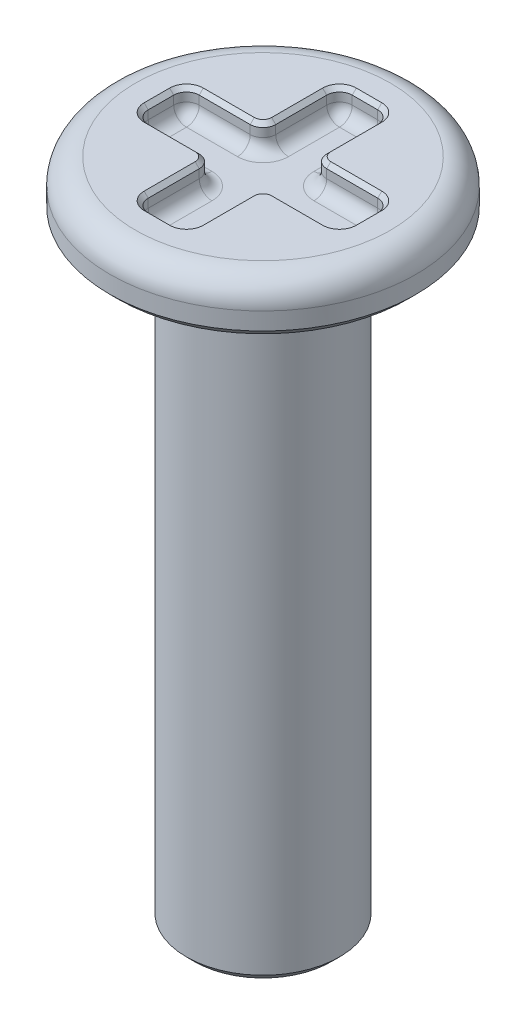
SolidWorks part; units mm, degrees
ref_plane "Front Plane" through (0, 0, 0) normal (0, 0, 1) x (1, 0, 0)
ref_plane "Top Plane" through (0, 0, 0) normal (0, 1, 0) x (1, 0, 0)
ref_plane "Right Plane" through (0, 0, 0) normal (1, 0, 0) x (0, 0, -1)
sketch "Sketch1" plane through (0, 0, 0) normal (0, 0, 1) x (1, 0, 0)
  line L0 (0, 5.1735) -> (0, 4.4648) construction
  line L1 (0, 0) -> (2.3813, 0)
  line L2 (2.3813, 0) -> (2.3813, 19.05)
  line L3 (2.3813, 19.05) -> (4.7625, 19.05)
  line L4 (4.7625, 19.05) -> (4.7625, 20.6375)
  line L5 (4.7625, 20.6375) -> (0, 20.6375)
  line L6 (0, 20.6375) -> (0, 0)
  dimension "D1" = 4.7625
  dimension "D2" = 19.05
  dimension "D3" = 1.5875
  dimension "D4" = 9.525
revolve "Revolve1" add sketch "Sketch1" angle 360 about L0
sketch "Sketch2" plane through (0, 20.6375, 0) normal (0, 1, 0) x (1, 0, 0)
  line L0 (-3.175, 0.7937) -> (-0.7938, 0.7937)
  line L1 (-0.7938, 0.7937) -> (-0.7937, 3.175)
  line L2 (-0.7937, 3.175) -> (0.7937, 3.175)
  line L3 (0.7937, 3.175) -> (0.7937, 0.7938)
  line L4 (0.7937, 0.7938) -> (3.175, 0.7937)
  line L5 (3.175, 0.7937) -> (3.175, -0.7937)
  line L6 (3.175, -0.7937) -> (0.7938, -0.7938)
  line L7 (0.7938, -0.7938) -> (0.7937, -3.175)
  line L8 (0.7937, -3.175) -> (-0.7937, -3.175)
  line L9 (-0.7937, -3.175) -> (-0.7938, -0.7938)
  line L10 (-0.7938, -0.7938) -> (-3.175, -0.7937)
  line L11 (-3.175, -0.7937) -> (-3.175, 0.7937)
  line L12 (0, -3.175) -> (0, 3.175) construction
  line L13 (3.175, 0) -> (-3.175, 0) construction
  dimension "D1" = 1.5875
  dimension "D2" = 6.35
extrude "Cut-Extrude1" cut sketch "Sketch2" against normal blind 0.7937 contours L1 L2 L3 L4 L5 L6 L7 L8 L9 L10 L11 L0
fillet "Fillet2" radius 0.7937 2 edges at (0, 20.6375, 4.7625) (0, 19.05, 2.3813)
fillet "Fillet3" radius 0.3969 24 edges at (-1.9844, 19.8438, -0.7937) (-0.7938, 19.8438, -1.9844) (0, 19.8438, -3.175) (0.7937, 19.8438, -1.9844) (1.9844, 19.8438, -0.7938) (3.175, 19.8438, 0) (1.9844, 19.8438, 0.7938) (0.7938, 19.8438, 1.9844) (0, 19.8438, 3.175) (-0.7938, 19.8438, 1.9844) (-1.9844, 19.8438, 0.7938) (-3.175, 19.8438, 0) (-3.175, 20.2406, -0.7937) (-3.175, 20.2406, 0.7937) (-0.7938, 20.2406, 0.7938) (-0.7937, 20.2406, 3.175) (0.7937, 20.2406, 3.175) (0.7938, 20.2406, 0.7938) (3.175, 20.2406, 0.7937) (3.175, 20.2406, -0.7937) (0.7937, 20.2406, -0.7938) (-0.7937, 20.2406, -3.175) (-0.7938, 20.2406, -0.7937) (0.7937, 20.2406, -3.175)
chamfer "Chamfer1" distance 0.254 angle 45 2 edges at (0, 0, 2.3813) (0, 19.05, 4.7625)
chamfer "Chamfer2" distance 0.127 angle 45 24 edges at (0.6775, 20.6375, 3.0588) (0.7938, 20.6375, 1.9844) (-0.6775, 20.6375, 3.0588) (0.91, 20.6375, 0.91) (-0.7938, 20.6375, 1.9844) (1.9844, 20.6375, 0.7938) (-0.91, 20.6375, 0.91) (3.0588, 20.6375, 0.6775) (-1.9844, 20.6375, 0.7938) (-3.0588, 20.6375, 0.6775) (3.0588, 20.6375, -0.6775) (1.9844, 20.6375, -0.7938) (-3.0588, 20.6375, -0.6775) (0.91, 20.6375, -0.91) (-1.9844, 20.6375, -0.7937) (0.7937, 20.6375, -1.9844) (-0.91, 20.6375, -0.91) (0.6775, 20.6375, -3.0588) (-0.7938, 20.6375, -1.9844) (-0.6775, 20.6375, -3.0588) (0, 20.6375, 3.175) (-3.175, 20.6375, 0) (3.175, 20.6375, 0) (0, 20.6375, -3.175)
